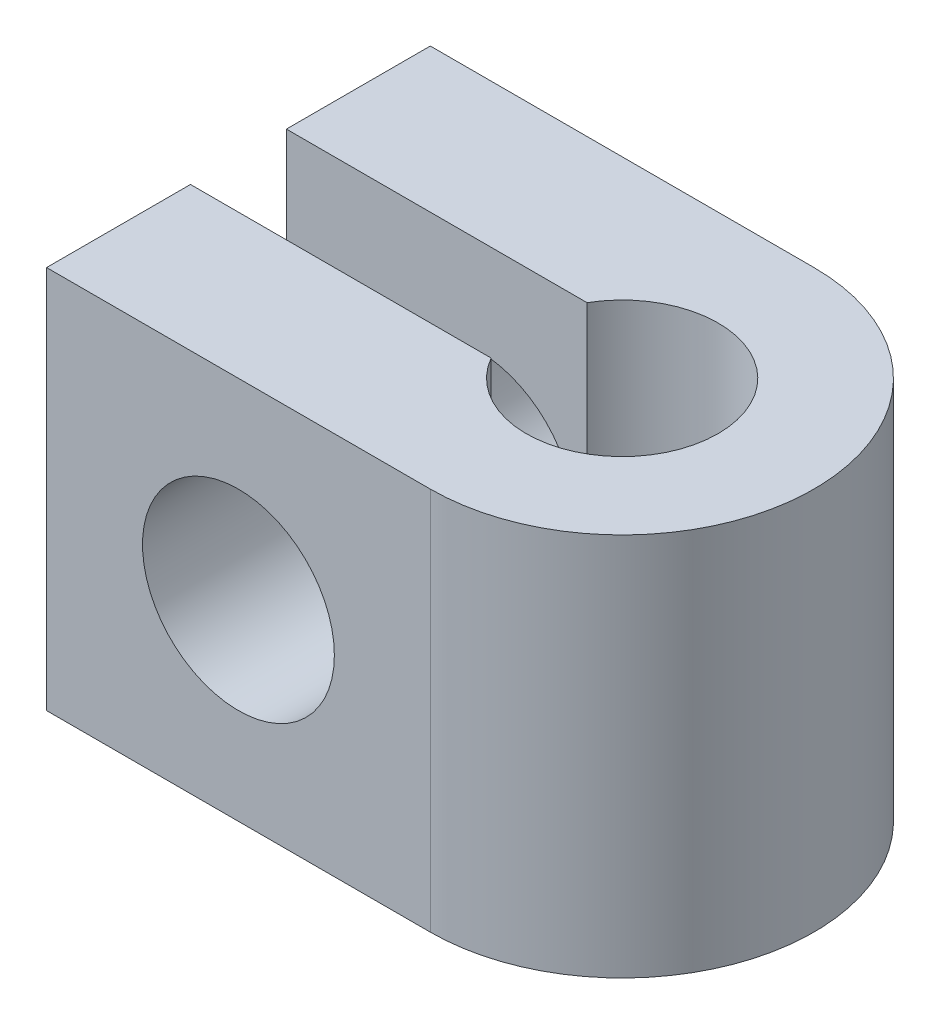
SolidWorks part; units mm, degrees
ref_plane "Front Plane" through (0, 0, 0) normal (0, 0, 1) x (1, 0, 0)
ref_plane "Top Plane" through (0, 0, 0) normal (0, 1, 0) x (1, 0, 0)
ref_plane "Right Plane" through (0, 0, 0) normal (1, 0, 0) x (0, 0, -1)
sketch "Sketch1" plane through (0, 0, 0) normal (0, 1, 0) x (1, 0, 0)
  line L0 (0, 0) -> (-12.7, 0)
  line L1 (-12.7, 0) -> (-12.7, -4.7625)
  line L2 (-12.7, -4.7625) -> (-2.7496, -4.7625)
  line L4 (-2.7496, -7.9375) -> (-12.7, -7.9375)
  line L5 (-12.7, -7.9375) -> (-12.7, -12.7)
  line L6 (-12.7, -12.7) -> (0, -12.7)
  arc A0 (0, 0) -> (0, -12.7) centre (0, -6.35) cw
  arc A1 (-2.7496, -4.7625) -> (-2.7496, -7.9375) centre (0, -6.35) cw
  dimension "D1" = 3.175
  dimension "D2" = 6.35
  dimension "D3" = 3.175
  dimension "D4" = 12.7
extrude "Boss-Extrude1" add sketch "Sketch1" along normal blind 12.7
sketch "Sketch2" plane through (0, 0, 12.7) normal (0, 0, 1) x (1, 0, 0)
  line L0 (0, 12.7) -> (0, 0) construction
  line L1 (-12.7, 12.7) -> (0, 12.7) construction
  circle A0 centre (-6.35, 6.35) radius 3.175
  point P4 (0, 6.35)
  point P7 (-6.35, 12.7)
  dimension "D1" = 6.35
extrude "Cut-Extrude1" cut sketch "Sketch2" against normal through all
